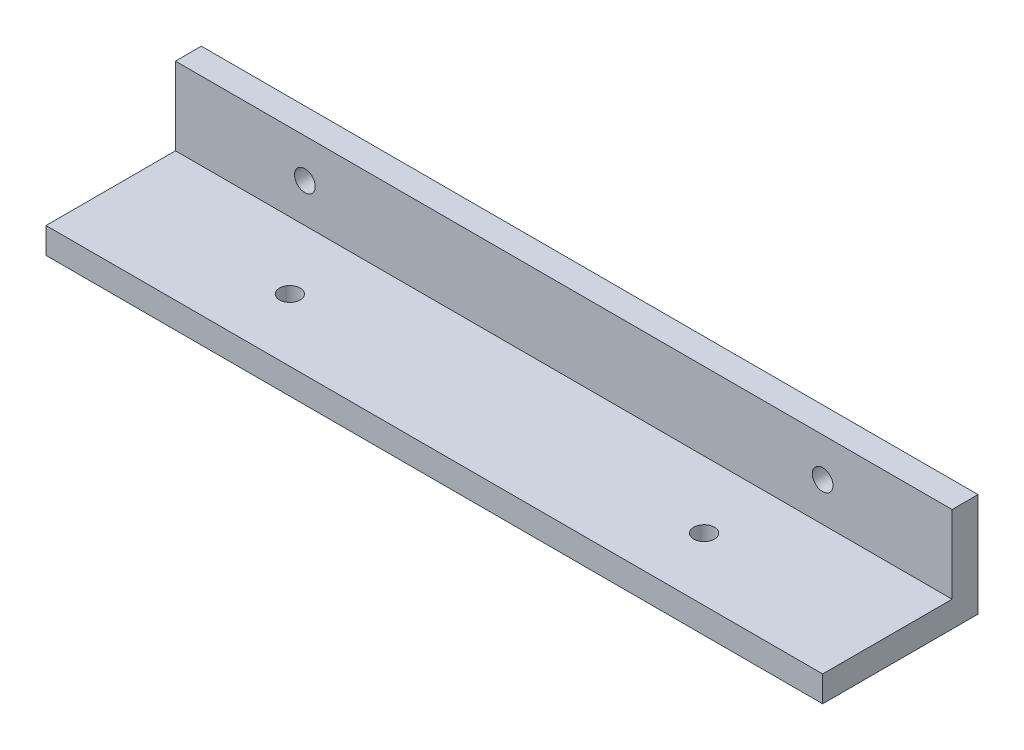
SolidWorks part; units mm, degrees
material "PET"
ref_plane "Front Plane" through (0, 0, 0) normal (0, 0, 1) x (1, 0, 0)
ref_plane "Top Plane" through (0, 0, 0) normal (0, 1, 0) x (1, 0, 0)
ref_plane "Right Plane" through (0, 0, 0) normal (1, 0, 0) x (0, 0, -1)
sketch "Sketch1" plane through (0, 0, 0) normal (0, 1, 0) x (1, 0, 0)
  line L1 (0, 0) -> (150, 0)
  line L2 (0, 0) -> (0, 20)
  line L3 (0, 20) -> (150, 20)
  line L4 (150, 0) -> (150, 20)
  dimension "D1" = 150
  dimension "D2" = 20
extrude "Boss-Extrude1" add sketch "Sketch1" against normal blind 5
sketch "Sketch3" plane through (0, 0, 0) normal (0, 1, 0) x (1, 0, 0)
  line L0 (150, 0) -> (150, 20) construction
  line L1 (0, 20) -> (150, 20)
  line L2 (0, 20) -> (0, 15)
  line L3 (0, 15) -> (150, 15)
  line L4 (150, 20) -> (150, 15)
  dimension "D1" = 5
extrude "Boss-Extrude2" add sketch "Sketch3" along normal blind 15
sketch "Sketch5" plane through (0, 0, -15) normal (0, 0, 1) x (1, 0, 0)
  line L0 (0, 15) -> (0, 0) construction
  line L1 (150, 15) -> (150, 0) construction
  line L2 (0, 0) -> (150, 0) construction
  circle A0 centre (25, 7.5) radius 2
  circle A1 centre (125, 7.5) radius 2
  dimension "D1" = 4
  dimension "D2" = 4
  dimension "D3" = 25
  dimension "D4" = 25
  dimension "D5" = 7.5
  dimension "D6" = 7.5
extrude "Cut-Extrude1" cut sketch "Sketch5" against normal through all
sketch "Sketch6" plane through (0, 0, 0) normal (0, 1, 0) x (1, 0, 0)
  line L1 (0, 15) -> (0, 0) construction
  line L3 (150, 0) -> (150, 15) construction
  line L4 (0, 0) -> (150, 0) construction
  circle A0 centre (35, 2.1) radius 2
  circle A1 centre (115, 2.1) radius 2
  dimension "D1" = 4
  dimension "D2" = 4
  dimension "D4" = 2.1
  dimension "D3" = 35
  dimension "D5" = 2.1
  dimension "D6" = 35
extrude "Cut-Extrude2" cut sketch "Sketch6" against normal through all
sketch "Sketch7" plane through (0, 0, 0) normal (0, 0, 1) x (1, 0, 0)
  line L1 (0, 0) -> (150, 0)
  line L2 (0, 0) -> (0, -5)
  line L3 (0, -5) -> (150, -5)
  line L4 (150, 0) -> (150, -5)
extrude "Boss-Extrude3" add sketch "Sketch7" along normal blind 10
